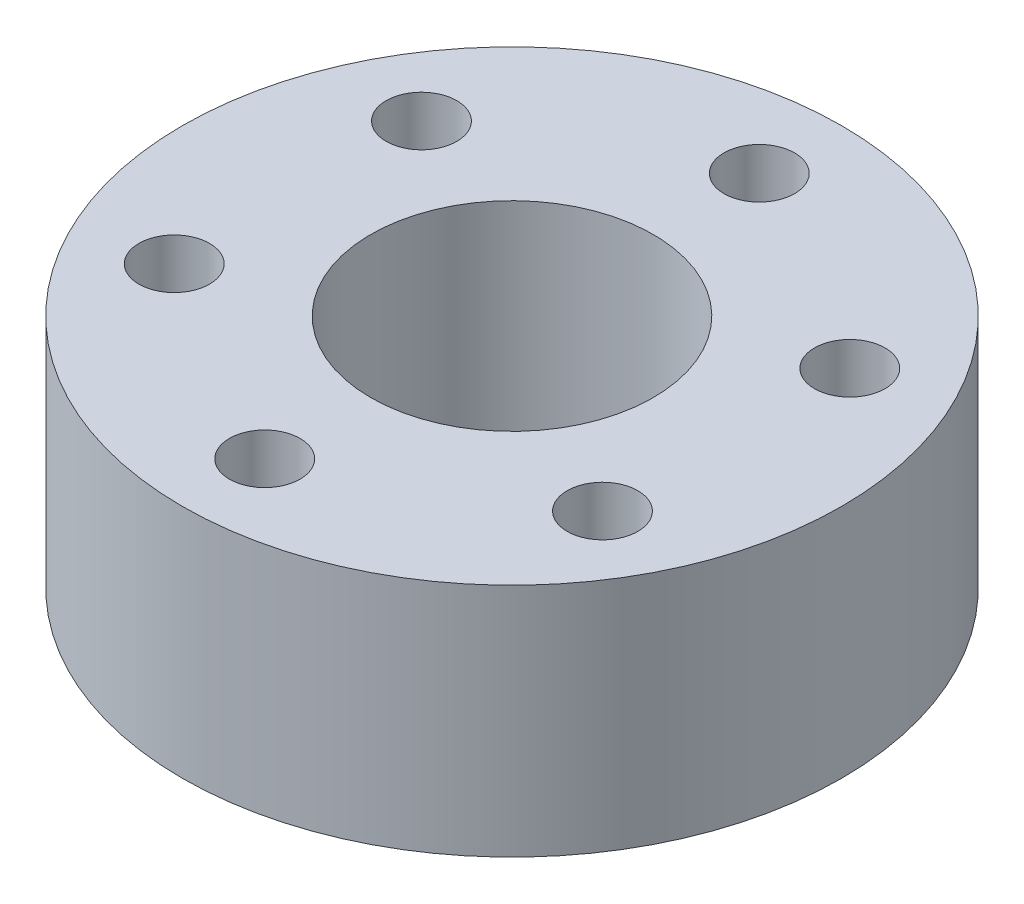
SolidWorks part; units mm, degrees
ref_plane "Front Plane" through (0, 0, 0) normal (0, 0, 1) x (1, 0, 0)
ref_plane "Top Plane" through (0, 0, 0) normal (0, 1, 0) x (1, 0, 0)
ref_plane "Right Plane" through (0, 0, 0) normal (1, 0, 0) x (0, 0, -1)
sketch "Sketch1" plane through (0, 0, 0) normal (0, 1, 0) x (1, 0, 0)
  circle A0 centre (0, 0) radius 14
  dimension "D1" = 28
extrude "Boss-Extrude1" add sketch "Sketch1" along normal blind 10
sketch "Sketch2" plane through (0, 10, 0) normal (0, 1, 0) x (1, 0, 0)
  line L0 (0, 0) -> (0, 50000) construction
  circle A0 centre (0, 0) radius 10.5 construction
  circle A1 centre (0, 10.5) radius 1.5
  circle A2 centre (0, 0) radius 6
  circle A3 centre (9.0933, 5.25) radius 1.5
  circle A4 centre (9.0933, -5.25) radius 1.5
  circle A5 centre (0, -10.5) radius 1.5
  circle A6 centre (-9.0933, -5.25) radius 1.5
  circle A7 centre (-9.0933, 5.25) radius 1.5
  point P18 (0, 0)
  dimension "D1" = 3
  dimension "D2" = 12
  dimension "D3" = 6
extrude "Cut-Extrude1" cut sketch "Sketch2" against normal through all
